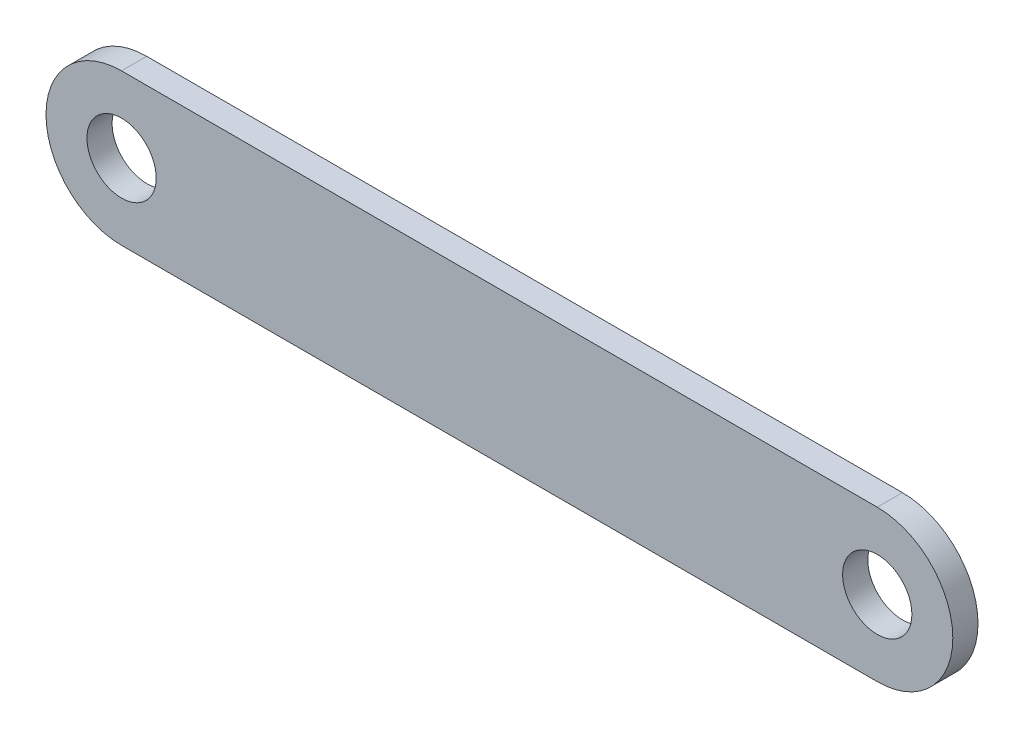
SolidWorks part; units mm, degrees
ref_plane "Front Plane" through (0, 0, 0) normal (0, 0, 1) x (1, 0, 0)
ref_plane "Top Plane" through (0, 0, 0) normal (0, 1, 0) x (1, 0, 0)
ref_plane "Right Plane" through (0, 0, 0) normal (1, 0, 0) x (0, 0, -1)
sketch "Sketch1" plane through (0, 0, 0) normal (0, 0, 1) x (1, 0, 0)
  line L0 (-30, 0) -> (30, 0) construction
  line L1 (-30, 6) -> (30, 6)
  line L2 (-30, -6) -> (30, -6)
  arc A0 (-30, 6) -> (-30, -6) centre (-30, 0) ccw
  arc A1 (30, -6) -> (30, 6) centre (30, 0) ccw
  circle A2 centre (30, 0) radius 2.75
  circle A3 centre (-30, 0) radius 2.75
  point P3 (0, 0)
  point P12 (0, 0)
  dimension "D2" = 6
  dimension "D3" = 5.5
  dimension "D4" = 5.5
  dimension "D1" = 60
extrude "Main" add sketch "Sketch1" along normal blind 2
